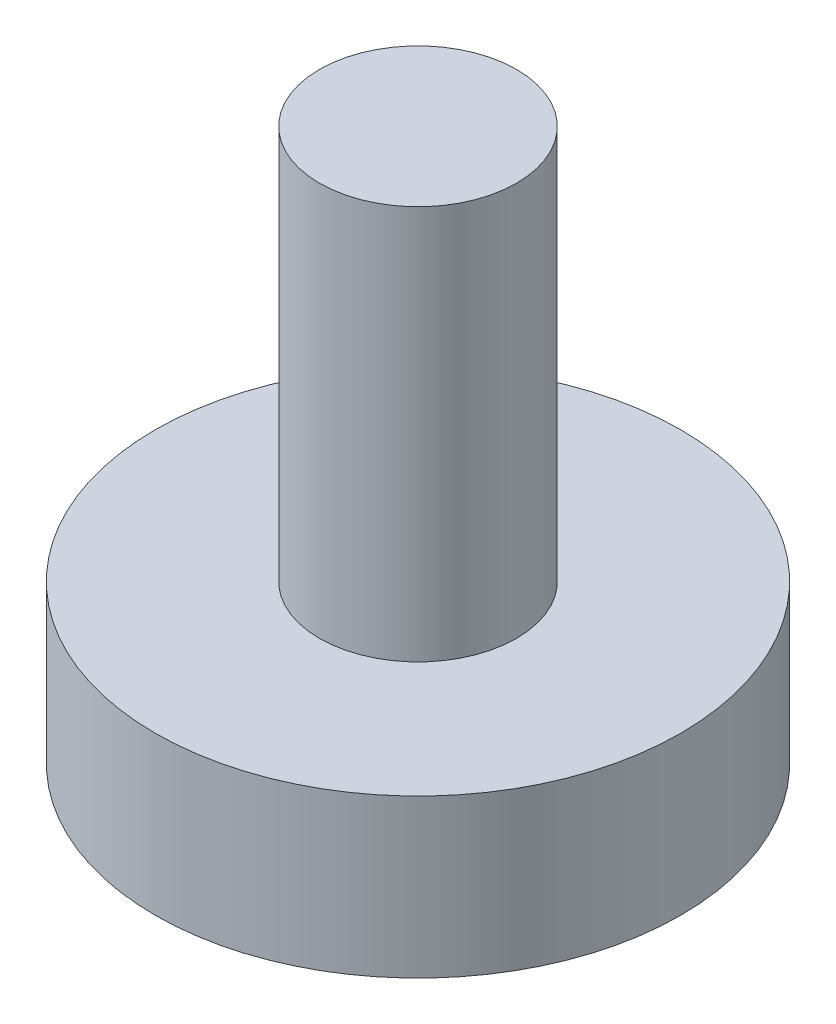
SolidWorks part; units mm, degrees
ref_plane "Alzado" through (0, 0, 0) normal (0, 0, 1) x (1, 0, 0)
ref_plane "Planta" through (0, 0, 0) normal (0, 1, 0) x (1, 0, 0)
ref_plane "Vista lateral" through (0, 0, 0) normal (1, 0, 0) x (0, 0, -1)
sketch "Croquis1" plane through (0, 0, 0) normal (0, 1, 0) x (1, 0, 0)
  circle A0 centre (0, 0) radius 10
  dimension "D1" = 20
extrude "Saliente-Extruir1" add sketch "Croquis1" along normal blind 6
sketch "Croquis2" plane through (0, 6, 0) normal (0, 1, 0) x (1, 0, 0)
  circle A0 centre (0, 0) radius 3.75
  dimension "D1" = 7.5
extrude "Saliente-Extruir2" add sketch "Croquis2" along normal blind 15
